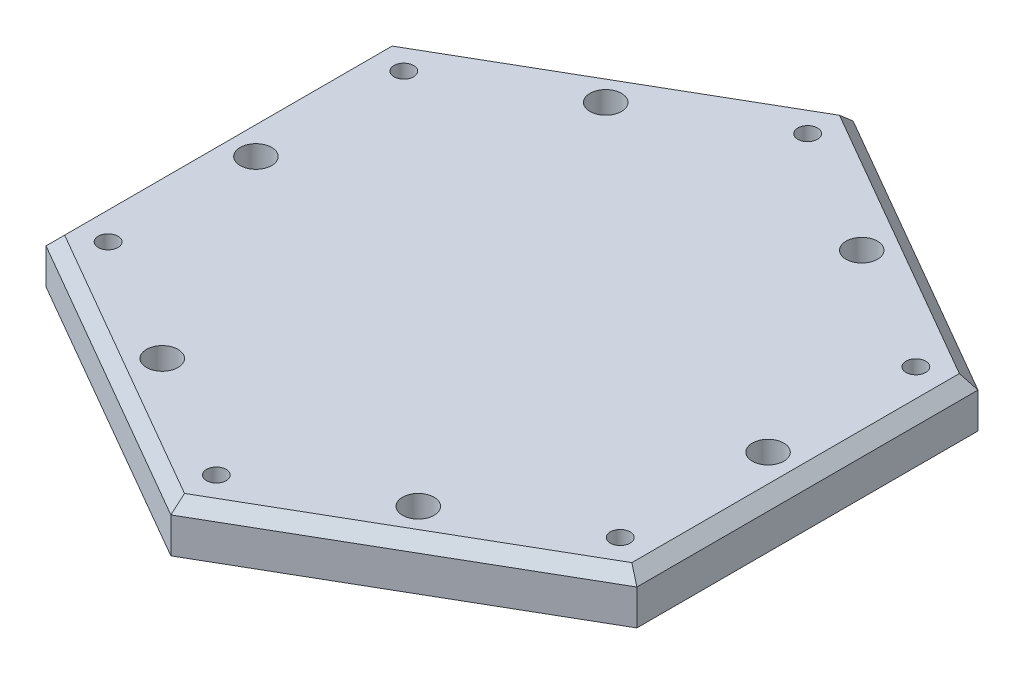
SolidWorks part; units mm, degrees
ref_plane "前基準面" through (0, 0, 0) normal (0, 0, 1) x (1, 0, 0)
ref_plane "上基準面" through (0, 0, 0) normal (0, 1, 0) x (1, 0, 0)
ref_plane "右基準面" through (0, 0, 0) normal (1, 0, 0) x (0, 0, -1)
sketch "草圖1" plane through (0, 0, 0) normal (0, 1, 0) x (1, 0, 0)
  line L1 (0, 86.6025) -> (-75, 43.3013)
  line L2 (-75, 43.3013) -> (-75, -43.3013)
  line L3 (-75, -43.3013) -> (0, -86.6025)
  line L4 (0, -86.6025) -> (75, -43.3013)
  line L5 (75, -43.3013) -> (75, 43.3013)
  line L6 (75, 43.3013) -> (0, 86.6025)
  circle A0 centre (0, 0) radius 75 construction
  point P1 (0, 0)
  point P10 (0, 0)
  dimension "D1" = 150
extrude "填料-伸長1" add sketch "草圖1" along normal blind 12
chamfer "導角1" distance 3 angle 45 6 edges at (75, 12, 0) (37.5, 12, 64.9519) (-37.5, 12, 64.9519) (-75, 12, 0) (-37.5, 12, -64.9519) (37.5, 12, -64.9519)
sketch "草圖2" plane through (0, 12, 0) normal (0, 1, 0) x (1, 0, 0)
  line L1 (0, 75.0555) -> (-65, 37.5278)
  line L2 (-65, 37.5278) -> (-65, -37.5278)
  line L3 (-65, -37.5278) -> (0, -75.0555)
  line L4 (0, -75.0555) -> (65, -37.5278)
  line L5 (65, -37.5278) -> (65, 37.5278)
  line L6 (65, 37.5278) -> (0, 75.0555)
  circle A0 centre (0, 0) radius 65 construction
  circle A1 centre (32.5, 56.2917) radius 4
  circle A2 centre (32.5, -56.2917) radius 4
  circle A3 centre (65, 0) radius 4
  circle A4 centre (-65, 0) radius 4
  circle A5 centre (-32.5, 56.2917) radius 4
  circle A6 centre (-32.5, -56.2917) radius 4
  dimension "D2" = 8
  dimension "D3" = 65
  dimension "D1" = 130
extrude "除料-伸長1" cut sketch "草圖2" against normal through all contours A4 | A5 | A1 | A3 | A2 | A6
hole_wizard "M6x1.0 螺紋孔1" positions "3D草圖1" profile "草圖3" tap size "M6x1.0" standard "Ansi Metric" end condition through all
sketch3d "3D草圖1"
  point P0 (-65, 12, -37.5278)
  point P3 (0, 12, -75.0555)
  point P6 (65, 12, -37.5278)
  point P9 (65, 12, 37.5278)
  point P12 (0, 12, 75.0555)
  point P15 (-65, 12, 37.5278)
sketch "草圖3" plane through (-65, 12, -37.5278) normal (1, 0, 0) x (0, 0, 1)
  line L0 (0, 0) -> (0, 12)
  line L1 (0, 12) -> (2.5, 12)
  line L2 (2.5, 12) -> (2.5, 0)
  line L5 (2.5, 0) -> (0, 0)
  line L11 (0, -6.35) -> (0, 107.95) construction
  dimension "砮 脸ふ苝 畖" = 5
  dimension "砮 脸ふ苝瞏 " = 12
cosmetic thread "鑽孔螺紋1" parameters "D2"=6
cosmetic thread "鑽孔螺紋2" parameters "D2"=6
cosmetic thread "鑽孔螺紋3" parameters "D2"=6
cosmetic thread "鑽孔螺紋4" parameters "D2"=6
cosmetic thread "鑽孔螺紋5" parameters "D2"=6
cosmetic thread "鑽孔螺紋6" parameters "D2"=6
